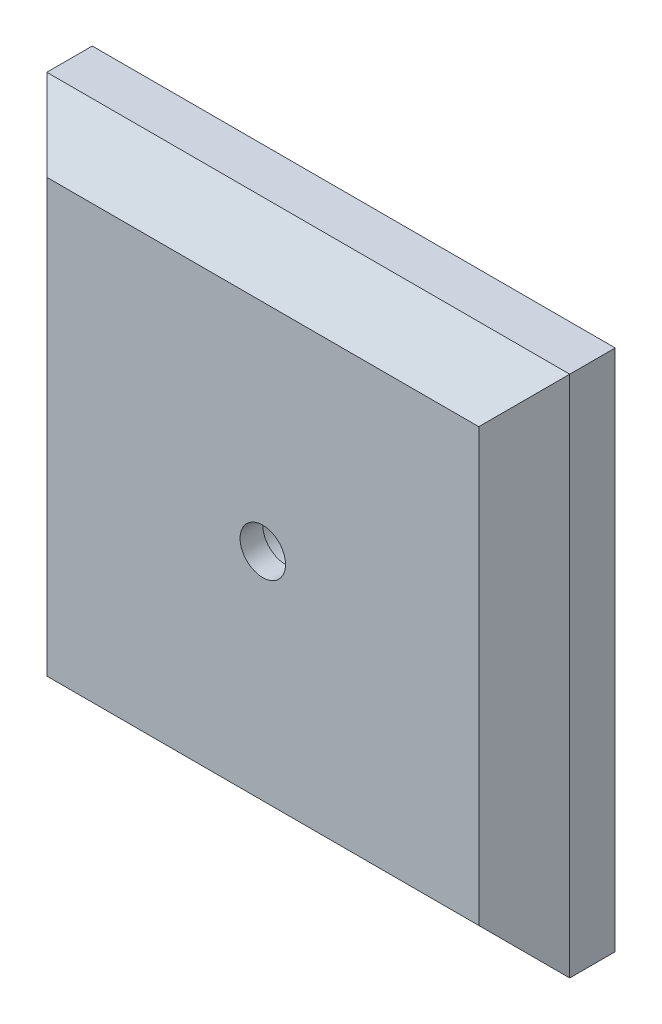
SolidWorks part; units mm, degrees
material "Plain Carbon Steel"
ref_plane "Front Plane" through (0, 0, 0) normal (0, 0, 1) x (1, 0, 0)
ref_plane "Top Plane" through (0, 0, 0) normal (0, 1, 0) x (1, 0, 0)
ref_plane "Right Plane" through (0, 0, 0) normal (1, 0, 0) x (0, 0, -1)
sketch "Sketch1" plane through (0, 0, 0) normal (0, 0, 1) x (1, 0, 0)
  line L1 (36.5125, -36.5125) -> (-36.5125, -36.5125)
  line L2 (36.5125, -36.5125) -> (36.5125, 36.5125)
  line L3 (36.5125, 36.5125) -> (-36.5125, 36.5125)
  line L4 (-36.5125, -36.5125) -> (-36.5125, 36.5125)
  line L5 (36.5125, -36.5125) -> (-36.5125, 36.5125) construction
  line L6 (36.5125, 36.5125) -> (-36.5125, -36.5125) construction
  point P0 (0, 0)
  dimension "D1" = 73.025
  dimension "D2" = 73.025
extrude "Boss-Extrude1" add sketch "Sketch1" against normal blind 12.7
sketch "Sketch2" plane through (0, 0, 0) normal (0, 0, 1) x (1, 0, 0)
  circle A0 centre (0, 0) radius 3.175
  circle A1 centre (0, 0) radius 6.35
  dimension "D1" = 6.35
  dimension "D2" = 12.7
extrude "Cut-Extrude1" cut sketch "Sketch2" against normal blind 3.175 contours A0
sketch "Sketch3" plane through (0, 0, -3.175) normal (0, 0, 1) x (1, 0, 0)
  circle A2 centre (0, 0) radius 4.7625
  dimension "D1" = 9.525
extrude "Cut-Extrude2" cut sketch "Sketch3" against normal through all
chamfer "Chamfer1" distance 6.35 4 edges at (-36.5125, 0, 0) (0, 36.5125, 0) (36.5125, 0, 0) (0, -36.5125, 0)
